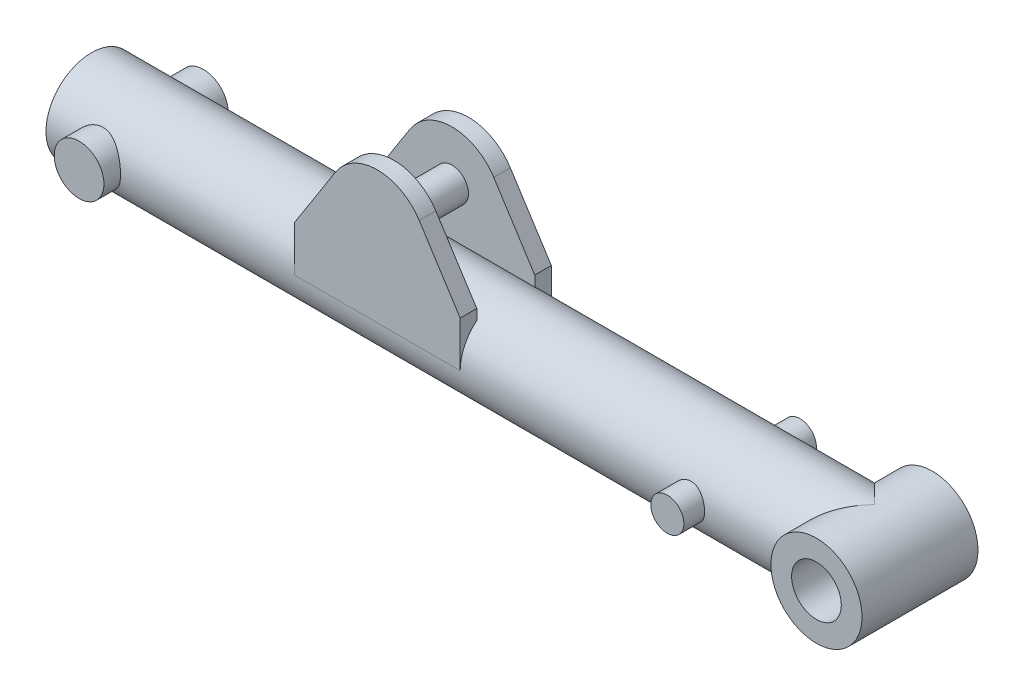
SolidWorks part; units mm, degrees
material "AISI 4340 Steel, normalized"
ref_plane "Front Plane" through (0, 0, 0) normal (0, 0, 1) x (1, 0, 0)
ref_plane "Top Plane" through (0, 0, 0) normal (0, 1, 0) x (1, 0, 0)
ref_plane "Right Plane" through (0, 0, 0) normal (1, 0, 0) x (0, 0, -1)
sketch "Sketch1" plane through (0, 0, 0) normal (1, 0, 0) x (0, 0, -1)
  circle A0 centre (0, 0) radius 55
  dimension "D1" = 110
extrude "Boss-Extrude1" add sketch "Sketch1" along normal blind 1000
shell "Shell1" thickness 10
sketch "Sketch2" plane through (0, 0, 0) normal (0, 0, 1) x (1, 0, 0)
  circle A0 centre (60, 0) radius 30
  dimension "D1" = 60
  dimension "D2" = 60
ref_plane "Plane1" through (0, 0, 55) normal (0, 0, 1) x (1, 0, 0)
sketch "Sketch3" plane through (0, 0, 55) normal (0, 0, 1) x (1, 0, 0)
  line L0 (300, 0) -> (300, 55)
  line L1 (500, 55) -> (450.5469, 132.3266)
  line L3 (300, 0) -> (500, 0)
  line L4 (500, 0) -> (500, 55)
  line L6 (1000, -55) -> (1000, 55) construction
  line L7 (300, 55) -> (349.4531, 132.3266)
  line L8 (1000, 55) -> (0, 55) construction
  arc A0 (450.5469, 132.3266) -> (349.4531, 132.3266) centre (400, 100) ccw
  circle A1 centre (400, 100) radius 20 construction
  point P14 (400, 0)
  dimension "D1" = 40
  dimension "D2" = 40
  dimension "D3" = 100
  dimension "D4" = 500
  dimension "D5" = 200
extrude "Boss-Extrude2" add sketch "Sketch3" against normal blind 20 separate body
sketch "Sketch4" plane through (1000, 0, 0) normal (1, 0, 0) x (0, 0, -1)
  line L0 (0, 55) -> (0, -55) construction
  circle A0 centre (0, 0) radius 55 construction
ref_plane "Plane2" through (0, 0, 0) normal (0, 0, 1) x (1, 0, 0)
mirror "Mirror2" about plane through (0, 0, 0) normal (0, 0, 1) of "Boss-Extrude2"
sketch "Sketch5" plane through (0, 0, 0) normal (0, 0, 1) x (1, 0, 0)
  line L0 (60.5, 0) -> (-60.5, 0) construction
  line L1 (1000, 55) -> (0, 55) construction
  line L2 (1000, -55) -> (1000, 55) construction
  circle A0 centre (945, 0) radius 55
extrude "Boss-Extrude3" add sketch "Sketch5" along normal mid plane 140
sketch "Sketch6" plane through (0, 0, 70) normal (0, 0, 1) x (1, 0, 0)
  line L0 (1000, 55) -> (1000, -55)
  line L1 (1000, -55) -> (1000, 0) construction
  line L2 (1000, -55) -> (945, -55)
  line L3 (1000, 55) -> (945, 55)
  circle A0 centre (945, 0) radius 30
  arc A1 (945, -55) -> (945, 55) centre (945, 0) ccw
  arc A2 (945, 55) -> (945, -55) centre (945, 0) ccw construction
  point P17 (775.7145, 15.5701)
  circle M3 centre (945, 0) radius 55
  dimension "D1" = 60
extrude "Cut-Extrude2" cut sketch "Sketch6" against normal through all contours A0 | L0 L3 M3 | L2 L0 M3
extrude "Boss-Extrude4" add sketch "Sketch2" along normal mid plane 150
sketch "Sketch7" plane through (0, 0, 0) normal (0, 0, 1) x (1, 0, 0)
  circle A1 centre (400, 100) radius 20 construction
  circle A2 centre (400, 100) radius 20
extrude "Boss-Extrude5" add sketch "Sketch7" along normal mid plane 110
sketch "Sketch8" plane through (0, 0, 0) normal (0, 0, 1) x (1, 0, 0)
  circle A0 centre (775, 0) radius 20
  point P2 (945, 0)
  dimension "D1" = 40
  dimension "D2" = 170
extrude "Boss-Extrude6" add sketch "Sketch8" along normal mid plane 160
